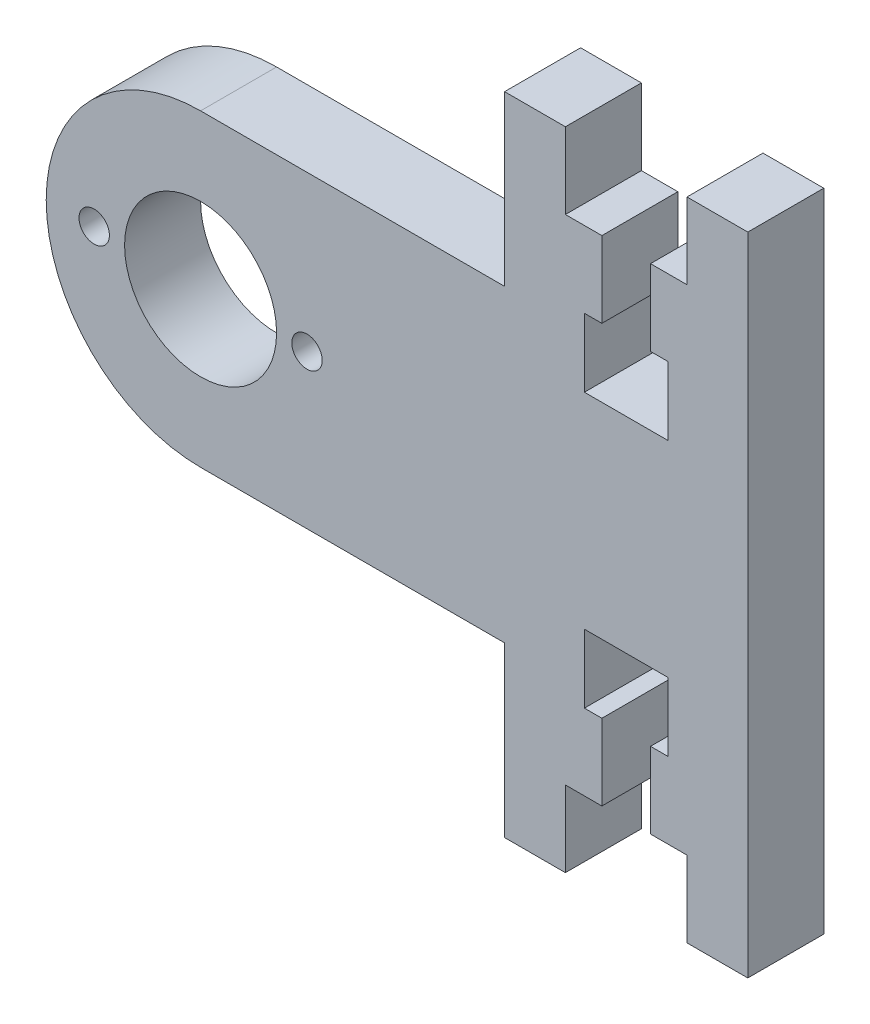
SolidWorks part; units mm, degrees
ref_plane "Front Plane" through (0, 0, 0) normal (0, 0, 1) x (1, 0, 0)
ref_plane "Top Plane" through (0, 0, 0) normal (0, 1, 0) x (1, 0, 0)
ref_plane "Right Plane" through (0, 0, 0) normal (1, 0, 0) x (0, 0, -1)
sketch "Sketch1" plane through (0, 0, 0) normal (0, 0, 1) x (1, 0, 0)
  line L40 (-36, 31.4062) -> (-16, 31.4062)
  line L41 (-16, 31.4062) -> (-16, 37.5)
  line L42 (-16, 5) -> (-16, 11.0937)
  line L43 (-16, 11.0937) -> (-36, 11.0938)
  line L44 (-46.1563, 21.25) -> (-44.123, 21.25) construction
  line L45 (-34.4766, 21.25) -> (-29.9043, 21.25) construction
  line L46 (-42.0957, 21.25) -> (-37.5234, 21.25) construction
  arc A0 (-36, 31.4062) -> (-36, 11.0938) centre (-36, 21.25) ccw
  line B0 (-11.2539, 0) -> (-16, 0)
  line B1 (-16, 0) -> (-16, 5)
  line B2 (-8.207, 5) -> (-10.7461, 5)
  line B3 (-11, 4.8242) -> (-11, 0.2539)
  line B4 (-11, 37.6758) -> (-11, 42.2461)
  line B5 (-8.207, 37.5) -> (-10.7461, 37.5)
  line B6 (-16, 42.5) -> (-16, 37.5)
  line B7 (-11.2539, 42.5) -> (-16, 42.5)
  line B8 (-8.207, 5) -> (-5, 5)
  line B9 (-5, 5) -> (-5, 0)
  line B10 (-5, 0) -> (0, 0)
  line B11 (0, 0) -> (0, 42.5)
  line B12 (0, 42.5) -> (-5, 42.5)
  line B13 (-5, 42.5) -> (-5, 37.5)
  line B14 (-5, 37.5) -> (-8.207, 37.5)
  line B15 (-11, 0.2539) -> (-11, 0)
  line B16 (-11, 0) -> (-11.2539, 0)
  line B17 (-11.2539, 42.5) -> (-11, 42.5)
  line B18 (-11, 42.5) -> (-11, 42.2461)
  line B19 (-11, 37.6758) -> (-11, 37.5)
  line B20 (-11, 37.5) -> (-10.7461, 37.5)
  line B21 (-10.7461, 5) -> (-11, 5)
  line B22 (-11, 5) -> (-11, 4.8242)
sketch_block_instance "Block3-2"
sketch_block "Block3" parameters "D1"=21.25, "D2"=16.25, "D3"=5, "D4"=6, "D5"=6, "D6"=5
extrude "Boss-Extrude1" add sketch "Sketch1" along normal blind 5
sketch "Sketch2" plane through (0, 0, 0) normal (0, 0, -1) x (-1, 0, 0)
  arc A4 (36, 11.0938) -> (36, 31.4062) centre (36, 21.25) ccw construction
  point P6 (46.1562, 21.25)
  circle B0 centre (36, 21.25) radius 5
  circle B1 centre (43, 21.3125) radius 1
  circle B2 centre (36.0625, 14.25) radius 1
  circle B3 centre (29, 21.1875) radius 1
  circle B4 centre (35.9375, 28.25) radius 1
sketch_block_instance "Block1-1"
sketch_block "Block1" parameters "D1"=2, "D2"=10
extrude "Cut-Extrude1" cut sketch "Sketch2" against normal blind 10
sketch "Sketch3" plane through (0, 0, 0) normal (0, 0, -1) x (-1, 0, 0)
  circle A0 centre (35.9375, 28.25) radius 1
  circle A1 centre (36.0625, 14.25) radius 1.4405
extrude "Boss-Extrude2" add sketch "Sketch3" against normal up to vertex (5 mm away)
sketch "Sketch4" plane through (0, 0, 5) normal (0, 0, 1) x (1, 0, 0)
  line L0 (-5, 5) -> (-11, 5) construction
  line L1 (-9.6, 5) -> (-6.4, 5)
  line L2 (-9.6, 5) -> (-9.6, 10)
  line L4 (-6.4, 5) -> (-6.4, 10)
  line L5 (-9.6, 10) -> (-10.75, 10)
  line L6 (-5.25, 10) -> (-6.4, 10)
  line L7 (-5.25, 10) -> (-5.25, 14.5)
  line L8 (-5.25, 14.5) -> (-10.75, 14.5)
  line L9 (-10.75, 10) -> (-10.75, 14.5)
  line L10 (0, 21.25) -> (-19.6554, 21.25) construction
  line L11 (0, 0) -> (0, 42.5) construction
  line L12 (-10.75, 32.5) -> (-10.75, 28)
  line L13 (-5.25, 28) -> (-10.75, 28)
  line L14 (-5.25, 32.5) -> (-5.25, 28)
  line L15 (-5.25, 32.5) -> (-6.4, 32.5)
  line L16 (-9.6, 32.5) -> (-10.75, 32.5)
  line L17 (-6.4, 37.5) -> (-6.4, 32.5)
  line L18 (-9.6, 37.5) -> (-9.6, 32.5)
  line L19 (-9.6, 37.5) -> (-6.4, 37.5)
  dimension "D2" = 5
  dimension "D3" = 5.5
  dimension "D4" = 4.5
extrude "Cut-Extrude2" cut sketch "Sketch4" against normal blind 10
sketch "Sketch5" plane through (0, 0, 5) normal (0, 0, 1) x (1, 0, 0)
  line L0 (-5, 0) -> (0, 0) construction
  line L2 (-11, 0) -> (-16, 0) construction
  line L3 (-5, 5) -> (-4, 5)
  line L4 (-5, 5) -> (-5, 0)
  line L5 (-5, 0) -> (-4, 0)
  line L6 (-4, 5) -> (-4, 0)
  line L7 (-11, 5) -> (-12, 5)
  line L8 (-11, 5) -> (-11, 0)
  line L9 (-11, 0) -> (-12, 0)
  line L10 (-12, 5) -> (-12, 0)
  line L11 (0, 21.25) -> (-14.1921, 21.25) construction
  line L12 (0, 0) -> (0, 42.5) construction
  line L13 (-12, 37.5) -> (-12, 42.5)
  line L14 (-11, 42.5) -> (-12, 42.5)
  line L15 (-11, 37.5) -> (-11, 42.5)
  line L16 (-11, 37.5) -> (-12, 37.5)
  line L17 (-4, 37.5) -> (-4, 42.5)
  line L18 (-5, 42.5) -> (-4, 42.5)
  line L19 (-5, 37.5) -> (-5, 42.5)
  line L20 (-5, 37.5) -> (-4, 37.5)
extrude "Cut-Extrude3" cut sketch "Sketch5" against normal blind 10
